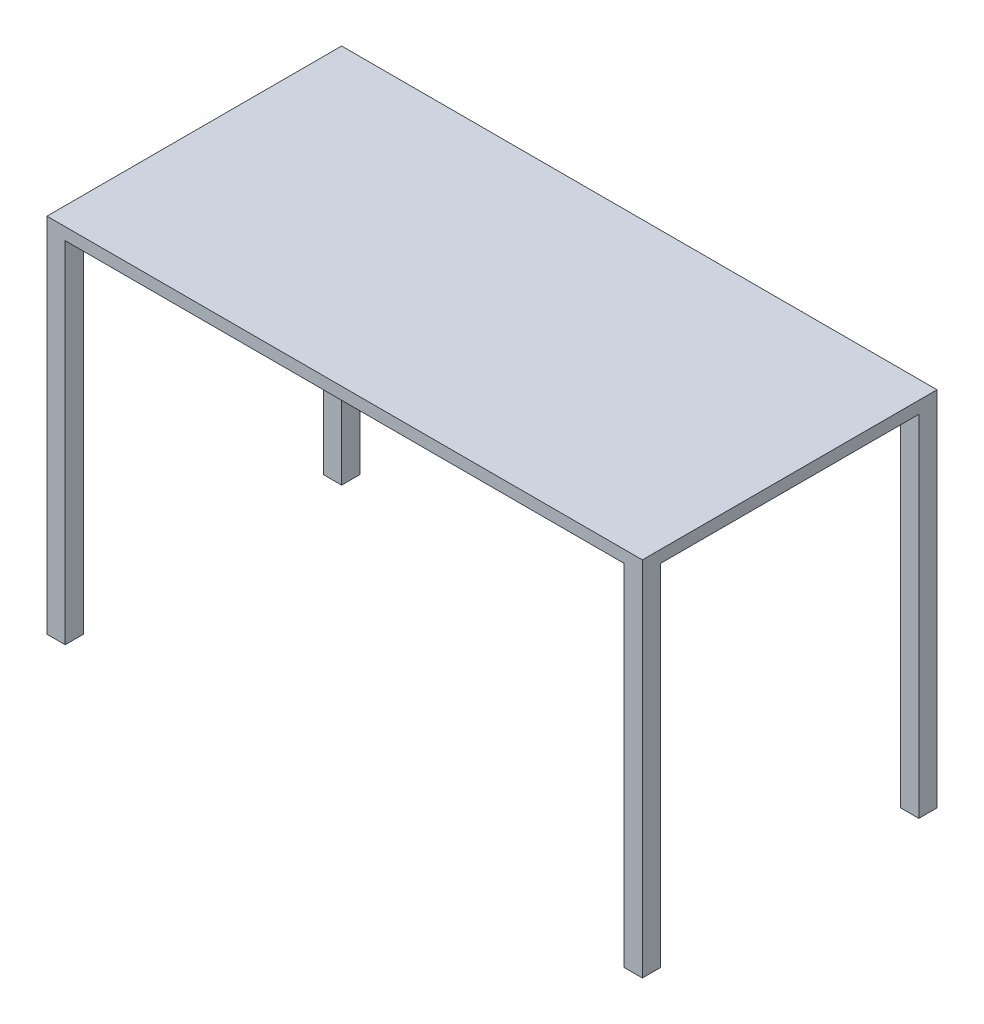
SolidWorks part; units mm, degrees
ref_plane "Front Plane" through (0, 0, 0) normal (0, 0, 1) x (1, 0, 0)
ref_plane "Top Plane" through (0, 0, 0) normal (0, 1, 0) x (1, 0, 0)
ref_plane "Right Plane" through (0, 0, 0) normal (1, 0, 0) x (0, 0, -1)
sketch "Sketch1" plane through (0, 0, 0) normal (0, 1, 0) x (1, 0, 0)
  line L1 (-622.3, -307.975) -> (622.3, -307.975)
  line L2 (-622.3, -307.975) -> (-622.3, 307.975)
  line L3 (-622.3, 307.975) -> (622.3, 307.975)
  line L4 (622.3, -307.975) -> (622.3, 307.975)
  line L5 (-622.3, -307.975) -> (622.3, 307.975) construction
  line L6 (-622.3, 307.975) -> (622.3, -307.975) construction
  point P0 (0, 0)
  dimension "D1" = 615.95
  dimension "D2" = 1244.6
extrude "Boss-Extrude1" add sketch "Sketch1" along normal blind 25.4
sketch "Sketch3" plane through (0, 0, 0) normal (0, -1, 0) x (1, 0, 0)
  line L0 (0, 307.975) -> (0, -374.1471) construction
  line L1 (-622.3, 307.975) -> (-584.2, 307.975)
  line L2 (-622.3, 307.975) -> (-622.3, 269.875)
  line L3 (-622.3, 269.875) -> (-584.2, 269.875)
  line L4 (-584.2, 307.975) -> (-584.2, 269.875)
  line L5 (-622.3, 307.975) -> (622.3, 307.975) construction
  line L6 (0, -374.1471) -> (622.3, 0) construction
  line L7 (622.3, 307.975) -> (622.3, -307.975) construction
  line L8 (622.3, 0) -> (-622.3, 0) construction
  line L9 (-622.3, -307.975) -> (-622.3, 307.975) construction
  line L10 (584.2, 307.975) -> (584.2, 269.875)
  line L11 (622.3, 269.875) -> (584.2, 269.875)
  line L12 (622.3, 307.975) -> (622.3, 269.875)
  line L13 (622.3, 307.975) -> (584.2, 307.975)
  line L14 (622.3, -307.975) -> (584.2, -307.975)
  line L15 (622.3, -307.975) -> (622.3, -269.875)
  line L16 (622.3, -269.875) -> (584.2, -269.875)
  line L17 (584.2, -307.975) -> (584.2, -269.875)
  line L18 (-584.2, -307.975) -> (-584.2, -269.875)
  line L19 (-622.3, -269.875) -> (-584.2, -269.875)
  line L20 (-622.3, -307.975) -> (-622.3, -269.875)
  line L21 (-622.3, -307.975) -> (-584.2, -307.975)
  dimension "D1" = 38.1
  dimension "D2" = 38.1
extrude "Boss-Extrude2" add sketch "Sketch3" along normal blind 731.52
